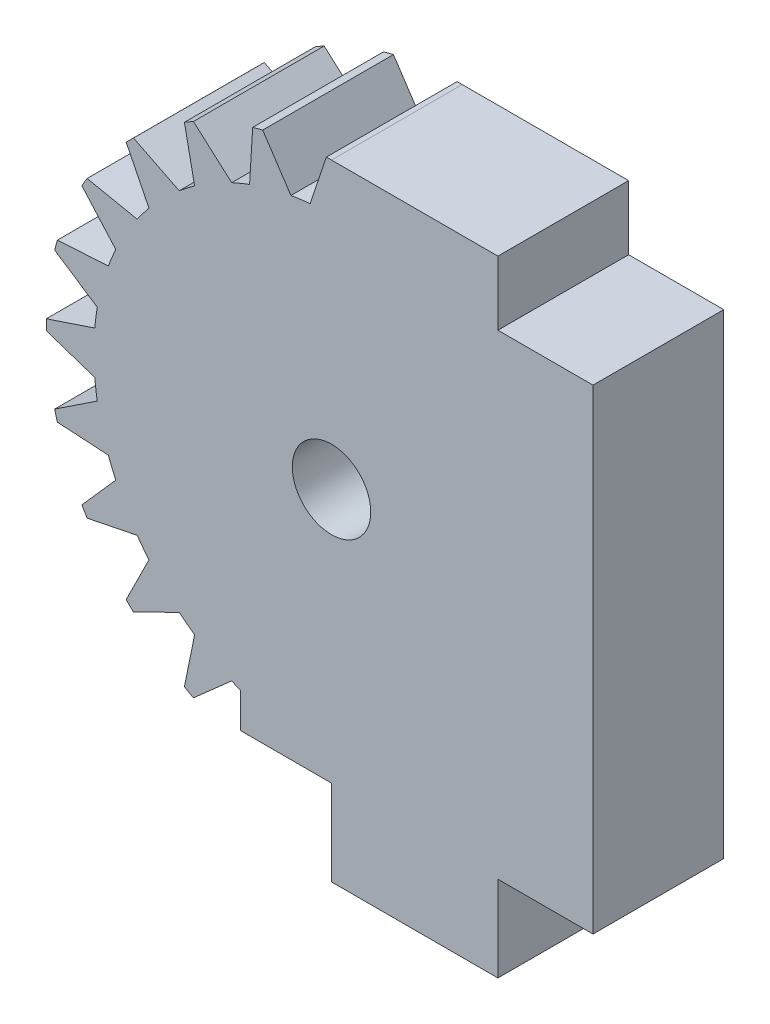
SolidWorks part; units mm, degrees
ref_plane "Front Plane" through (0, 0, 0) normal (0, 0, 1) x (1, 0, 0)
ref_plane "Top Plane" through (0, 0, 0) normal (0, 1, 0) x (1, 0, 0)
ref_plane "Right Plane" through (0, 0, 0) normal (1, 0, 0) x (0, 0, -1)
sketch "Sketch1" plane through (0, 0, 0) normal (0, 0, 1) x (1, 0, 0)
  circle A0 centre (0, 0) radius 10
  dimension "D1" = 20
extrude "Boss-Extrude1" add sketch "Sketch1" along normal blind 5.5
sketch "Sketch2" plane through (0, 0, 0) normal (0, 0, 1) x (1, 0, 0)
  line L2 (0, 12.65) -> (-0.9, 9.9594)
  line L3 (0, 12.65) -> (0.9, 9.9594)
  arc A0 (0.9, 9.9594) -> (-0.9, 9.9594) centre (0, 0) ccw
  dimension "D1" = 20
  dimension "D3" = 2.8371
  dimension "D4" = 1.8
extrude "Boss-Extrude2" add sketch "Sketch2" along normal blind 5.5
pattern_circular "CirPattern1" count 24 every 15 about axis through (0, 0, 0) along (0, 0, 1) of "Boss-Extrude2"
sketch "Sketch3" plane through (0, 0, 0) normal (0, 0, 1) x (1, 0, 0)
  circle A0 centre (0, 0) radius 12
  circle A1 centre (0, 0) radius 12.65
  dimension "D1" = 24
  dimension "D2" = 25.3
extrude "Cut-Extrude1" cut sketch "Sketch3" along normal blind 6
sketch "Sketch4" plane through (0, 0, 0) normal (0, 0, 1) x (1, 0, 0)
  line L0 (0, 0) -> (0, 12)
  line L2 (0, 0) -> (-3.8268, -9.2388)
  line L4 (-3.8268, -9.2388) -> (-4.5922, -11.0866)
  arc A0 (-4.5922, -11.0866) -> (0, 12) centre (0, 0) ccw
  arc A1 (0.2181, 11.998) -> (-0.2181, 11.998) centre (0, 0) ccw construction
  arc A2 (-4.2003, -9.0751) -> (-3.447, -9.3871) centre (0, 0) ccw construction
extrude "Cut-Extrude2" cut sketch "Sketch4" along normal blind 6
sketch "Sketch5" plane through (0, 0, 0) normal (0, 0, 1) x (1, 0, 0)
  circle A0 centre (0, 0) radius 1.65
  dimension "D1" = 3.3
extrude "Cut-Extrude3" cut sketch "Sketch5" along normal blind 6
sketch "Sketch6" plane through (0, 0, 0) normal (0, 0, 1) x (1, 0, 0)
  line L0 (0, 1.65) -> (0, 12)
  line L3 (11, 9.3) -> (7, 9.3)
  line L5 (7, 9.3) -> (7, 12)
  line L6 (11, -10.7) -> (11, 9.3)
  line L7 (11, -10.7) -> (7, -10.7)
  line L8 (7, -10.7) -> (7, -14.3)
  line L10 (0, 12) -> (7, 12)
  line L14 (7, -14.3) -> (0, -14.3)
  line L15 (-3.8268, -10.7) -> (0, -10.7)
  line L16 (0, -10.7) -> (0, -14.3)
  line L17 (-0.6314, -1.5244) -> (-3.8268, -9.2388)
  line L18 (-3.8268, -9.2388) -> (-3.8268, -10.7)
  arc A0 (-0.6314, -1.5244) -> (0, 1.65) centre (0, 0) ccw
  dimension "D2" = 2.7
  dimension "D6" = 7
  dimension "D4" = 20
  dimension "D5" = 4
  dimension "D7" = 3.6
  dimension "D8" = 7
  dimension "D11" = 4
extrude "Boss-Extrude3" add sketch "Sketch6" along normal blind 5.5
sketch "Sketch7" [suppressed] plane through (0, 0, 6) normal (0, 0, 1) x (1, 0, 0)
  line L0 (-0.2181, 11.998) -> (7, 12)
  line L1 (7, 12) -> (7, 9.9045)
  line L2 (7, 9.9045) -> (11, 9.9045)
  line L3 (11, 9.9045) -> (11, -10.0955)
  line L4 (11, -10.0955) -> (7, -10.0955)
  line L5 (7, -10.0955) -> (7, -13.0955)
  line L6 (7, -13.0955) -> (0, -13.0955)
  line L7 (0, -13.0955) -> (0, -10.0955)
  line L8 (0, -10.0955) -> (-3.8268, -10.0955)
  line L9 (-3.8268, -10.0955) -> (-3.8268, -9.2388)
  line L10 (-0.2181, 11.998) -> (-0.9, 9.9594)
  line L11 (-1.7084, 9.853) -> (-2.8947, 11.6456)
  line L12 (-2.8947, 11.6456) -> (-3.316, 11.5328)
  line L13 (-3.316, 11.5328) -> (-3.447, 9.3871)
  line L14 (-4.2003, 9.0751) -> (-5.8101, 10.4996)
  line L15 (-5.8101, 10.4996) -> (-6.1879, 10.2815)
  line L16 (-6.1879, 10.2815) -> (-5.7591, 8.1751)
  line L17 (-6.406, 7.6788) -> (-8.3297, 8.6381)
  line L18 (-8.3297, 8.6381) -> (-8.6381, 8.3297)
  line L19 (-8.6381, 8.3297) -> (-7.6788, 6.406)
  line L20 (-8.1751, 5.7591) -> (-10.2815, 6.1879)
  line L21 (-10.2815, 6.1879) -> (-10.4996, 5.8101)
  line L22 (-10.4996, 5.8101) -> (-9.0751, 4.2003)
  line L23 (-9.3871, 3.447) -> (-11.5328, 3.316)
  line L24 (-11.5328, 3.316) -> (-11.6456, 2.8947)
  line L25 (-11.6456, 2.8947) -> (-9.853, 1.7084)
  line L26 (-9.9594, 0.9) -> (-11.998, 0.2181)
  line L27 (-11.998, 0.2181) -> (-11.998, -0.2181)
  line L28 (-11.998, -0.2181) -> (-9.9594, -0.9)
  line L29 (-9.853, -1.7084) -> (-11.6456, -2.8947)
  line L30 (-11.6456, -2.8947) -> (-11.5328, -3.316)
  line L31 (-11.5328, -3.316) -> (-9.3871, -3.447)
  line L32 (-9.0751, -4.2003) -> (-10.4996, -5.8101)
  line L33 (-10.4996, -5.8101) -> (-10.2815, -6.1879)
  line L34 (-10.2815, -6.1879) -> (-8.1751, -5.7591)
  line L35 (-7.6788, -6.406) -> (-8.6381, -8.3297)
  line L36 (-7.6788, -6.406) -> (-8.6381, -8.3297) construction
  line L37 (-8.6381, -8.3297) -> (-8.3297, -8.6381)
  line L38 (-8.3297, -8.6381) -> (-6.406, -7.6788)
  line L39 (-5.7591, -8.1751) -> (-6.1879, -10.2815)
  line L40 (-6.1879, -10.2815) -> (-5.8101, -10.4996)
  line L41 (-5.8101, -10.4996) -> (-4.2003, -9.0751)
  circle A0 centre (0, 0) radius 1.5
  arc A1 (-0.9, 9.9594) -> (-1.7084, 9.853) centre (0, 0) ccw
  arc A2 (-3.447, 9.3871) -> (-4.2003, 9.0751) centre (0, 0) ccw
  arc A3 (-5.7591, 8.1751) -> (-6.406, 7.6788) centre (0, 0) ccw
  arc A4 (-7.6788, 6.406) -> (-8.1751, 5.7591) centre (0, 0) ccw
  arc A5 (-9.0751, 4.2003) -> (-9.3871, 3.447) centre (0, 0) ccw
  arc A6 (-9.853, 1.7084) -> (-9.9594, 0.9) centre (0, 0) ccw
  arc A7 (-4.2003, -9.0751) -> (-3.8268, -9.2388) centre (0, 0) ccw
  arc A8 (-6.406, -7.6788) -> (-5.7591, -8.1751) centre (0, 0) ccw
  arc A9 (-8.1751, -5.7591) -> (-7.6788, -6.406) centre (0, 0) ccw
  arc A10 (-9.3871, -3.447) -> (-9.0751, -4.2003) centre (0, 0) ccw
  arc A11 (-9.9594, -0.9) -> (-9.853, -1.7084) centre (0, 0) ccw
equation "\"D2@Sketch6\"= 2.1 + \"tol2@parametersSketch@prostheticParameters.SLDPRT\" * 2"
equation "\"D7@Sketch6\"= 3 + \"tol2@parametersSketch@prostheticParameters.SLDPRT\" * 2"
equation "\"D1@Boss-Extrude3\" = 5.8 - \"tol2@parametersSketch@prostheticParameters.SLDPRT\""
equation "\"D1@Boss-Extrude1\" = 5.8 - \"tol2@parametersSketch@prostheticParameters.SLDPRT\""
equation "\"D1@Boss-Extrude2\"= 5.8 - \"tol2@parametersSketch@prostheticParameters.SLDPRT\""
equation "\"D1@Sketch5\"= 3 + \"tol1@parametersSketch@prostheticParameters.SLDPRT\""
